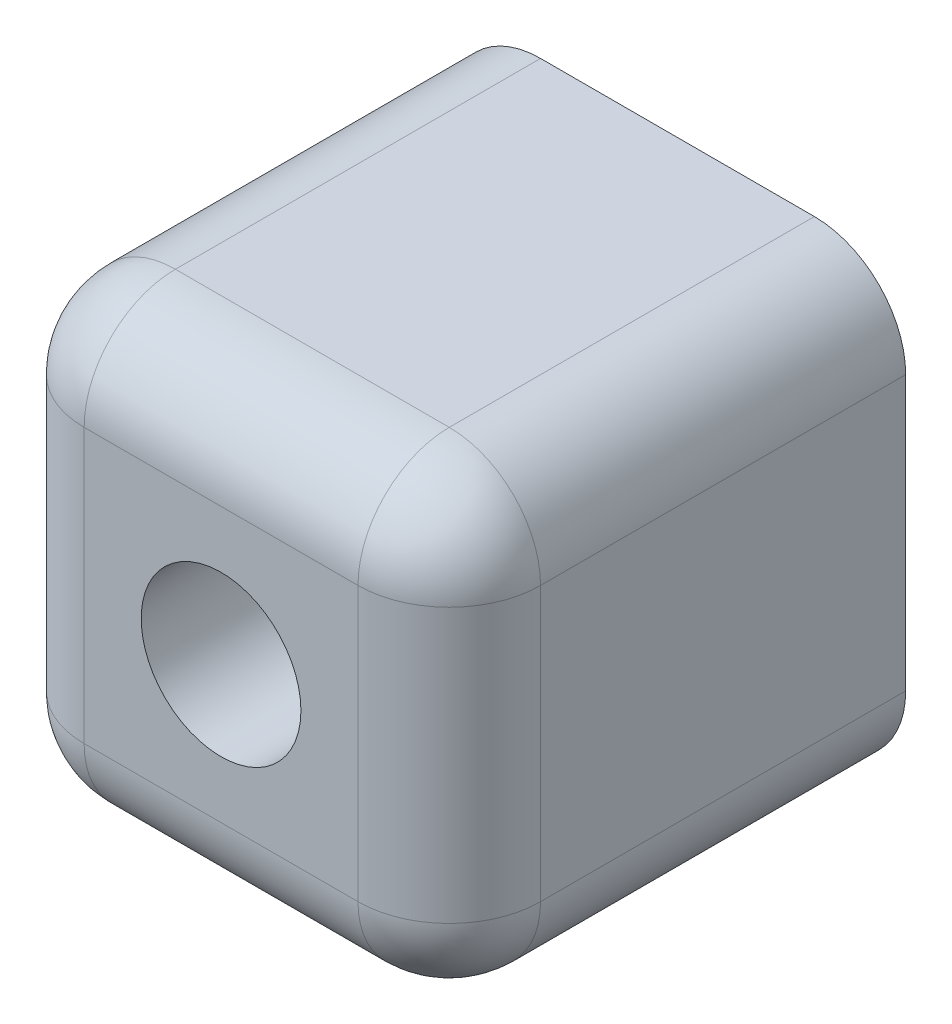
SolidWorks part; units mm, degrees
ref_plane "Front Plane" through (0, 0, 0) normal (0, 0, 1) x (1, 0, 0)
ref_plane "Top Plane" through (0, 0, 0) normal (0, 1, 0) x (1, 0, 0)
ref_plane "Right Plane" through (0, 0, 0) normal (1, 0, 0) x (0, 0, -1)
sketch "Sketch1" plane through (0, 0, 0) normal (0, 0, 1) x (1, 0, 0)
  line L1 (0, 0) -> (10, 0)
  line L2 (0, 0) -> (0, 10)
  line L3 (0, 10) -> (10, 10)
  line L4 (10, 0) -> (10, 10)
  dimension "D1" = 10
  dimension "D2" = 10
extrude "Boss-Extrude1" add sketch "Sketch1" along normal blind 10
sketch "Sketch2" plane through (0, 0, 10) normal (0, 0, 1) x (1, 0, 0)
  line L0 (0, 0) -> (10, 0) construction
  line L1 (0, 10) -> (0, 0) construction
  circle A0 centre (5, 5) radius 1.75
  dimension "D3" = 3.5
  dimension "D1" = 5
  dimension "D2" = 5
extrude "Cut-Extrude1" cut sketch "Sketch2" against normal through all
sketch "Sketch3" plane through (0, 0, 0) normal (0, 0, -1) x (-1, 0, 0)
  circle A0 centre (-5, 5) radius 2.304
  dimension "D1" = 4.608
extrude "Cut-Extrude2" cut sketch "Sketch3" against normal blind 5
fillet "Fillet1" radius 2 4 edges at (10, 10, 5) (0, 10, 5) (0, 0, 5) (10, 0, 5)
fillet "Fillet2" radius 2 8 edges at (0.5858, 0.5858, 10) (0, 5, 10) (0.5858, 9.4142, 10) (5, 10, 10) (9.4142, 9.4142, 10) (10, 5, 10) (9.4142, 0.5858, 10) (5, 0, 10)
